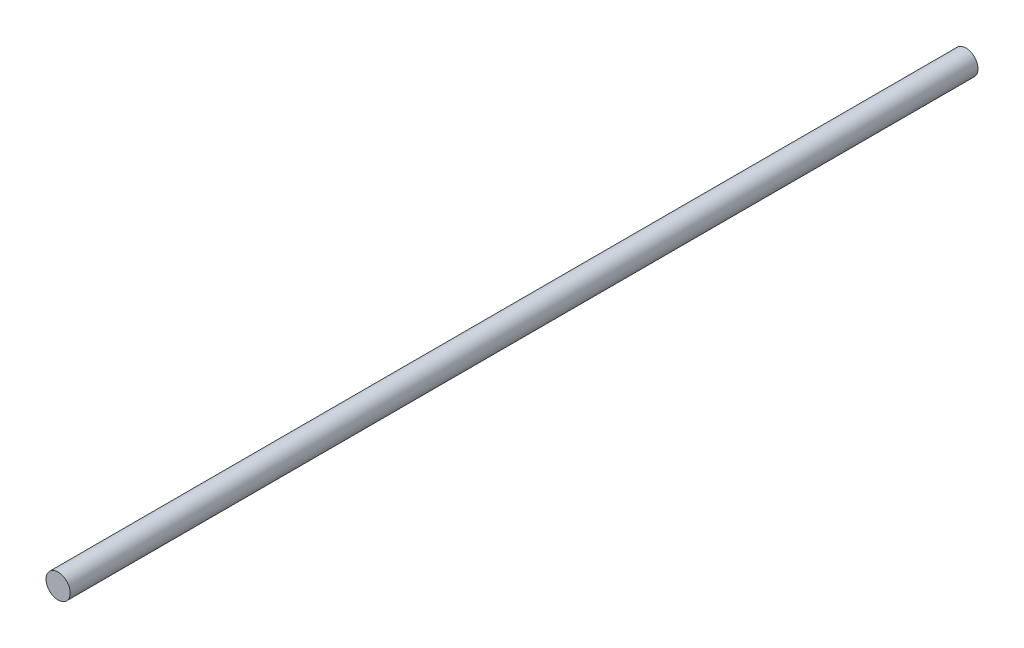
SolidWorks part; units mm, degrees
ref_plane "Plano frontal" through (0, 0, 0) normal (0, 0, 1) x (1, 0, 0)
ref_plane "Plano superior" through (0, 0, 0) normal (0, 1, 0) x (1, 0, 0)
ref_plane "Plano direito" through (0, 0, 0) normal (1, 0, 0) x (0, 0, -1)
sketch "Esboço1" plane through (0, 0, 0) normal (0, 0, 1) x (1, 0, 0)
  circle A0 centre (0, 0) radius 4
  dimension "D1" = 8
extrude "Ressalto-extrusão1" add sketch "Esboço1" along normal blind 300
